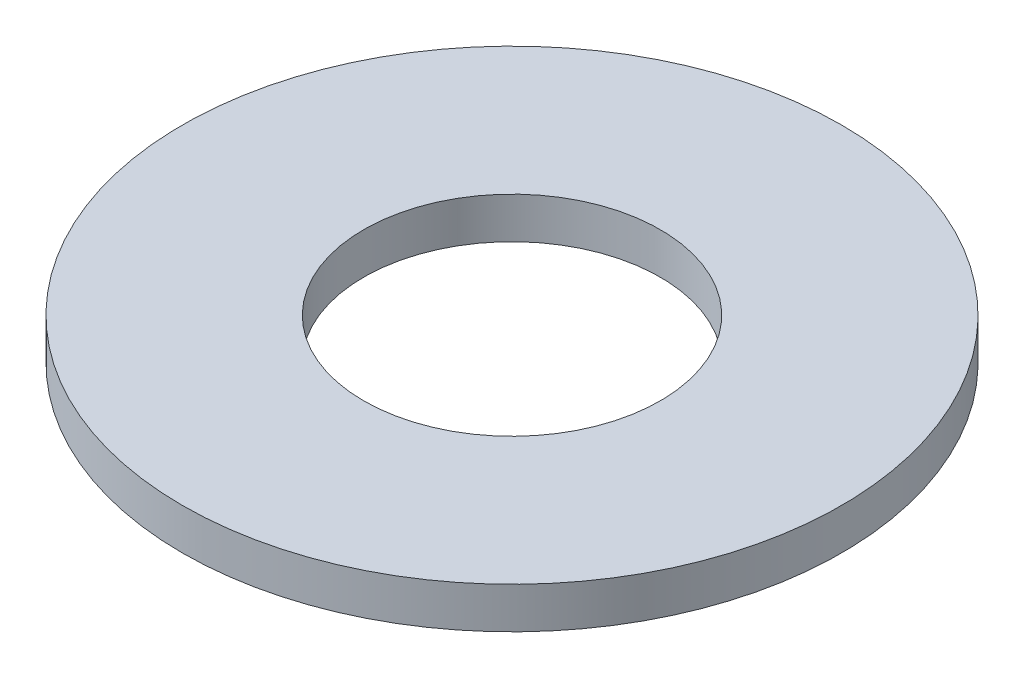
SolidWorks part; units mm, degrees
ref_plane "Front Plane" through (0, 0, 0) normal (0, 0, 1) x (1, 0, 0)
ref_plane "Top Plane" through (0, 0, 0) normal (0, 1, 0) x (1, 0, 0)
ref_plane "Right Plane" through (0, 0, 0) normal (1, 0, 0) x (0, 0, -1)
sketch "Sketch1" plane through (0, 0, 0) normal (0, 1, 0) x (1, 0, 0)
  circle A0 centre (0, 0) radius 1.8
  circle A1 centre (0, 0) radius 4
  dimension "D1" = 8
  dimension "D2" = 3.6
extrude "Boss-Extrude1" add sketch "Sketch1" along normal blind 0.5
